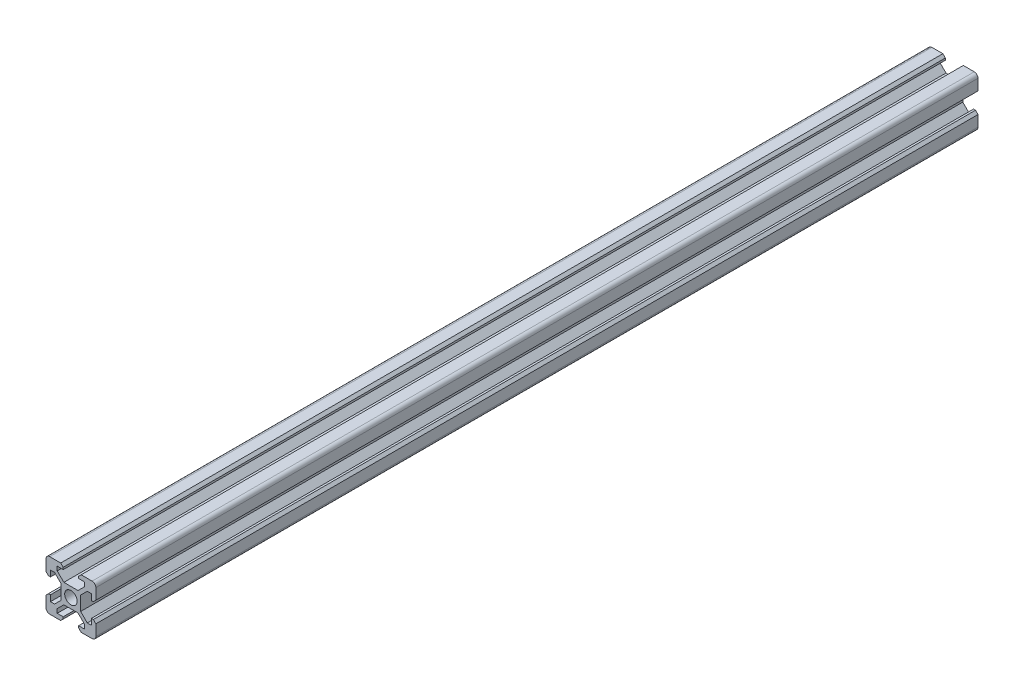
SolidWorks part; units mm, degrees
ref_plane "Front Plane" through (0, 0, 0) normal (0, 0, 1) x (1, 0, 0)
ref_plane "Top Plane" through (0, 0, 0) normal (0, 1, 0) x (1, 0, 0)
ref_plane "Right Plane" through (0, 0, 0) normal (1, 0, 0) x (0, 0, -1)
sketch "Sketch1" plane through (0, 0, 0) normal (0, 0, 1) x (1, 0, 0)
  line L0 (0, 16.1631) -> (0, -12.0251) construction
  line L1 (-21.8377, 0) -> (16.3885, 0) construction
  line L2 (2.8393, 3.9) -> (-2.8393, 3.9)
  line L3 (-2.8393, 3.9) -> (-5.5, 6.5607)
  line L4 (-5.5, 6.5607) -> (-5.5, 8.2)
  line L5 (-5.5, 8.2) -> (-3.1, 8.2)
  line L6 (-3.1, 8.2) -> (-3.1, 9)
  line L7 (-4.1, 10) -> (-8.5, 10)
  line L8 (-10, 8.5) -> (-10, 4.1)
  line L9 (-9, 3.1) -> (-8.2, 3.1)
  line L10 (-8.2, 3.1) -> (-8.2, 5.5)
  line L11 (-8.2, 5.5) -> (-6.5607, 5.5)
  line L12 (-6.5607, 5.5) -> (-3.9, 2.8393)
  line L13 (-3.9, 2.8393) -> (-3.9, -2.8393)
  line L14 (11.4015, -11.4015) -> (-14.8602, 14.8602) construction
  line L15 (-3.1, 9) -> (-4.1, 10)
  line L16 (-10, 4.1) -> (-9, 3.1)
  line L17 (-10, -4.1) -> (-9, -3.1)
  line L18 (-3.1, -9) -> (-4.1, -10)
  line L19 (-6.5607, -5.5) -> (-3.9, -2.8393)
  line L20 (-8.2, -5.5) -> (-6.5607, -5.5)
  line L21 (-8.2, -3.1) -> (-8.2, -5.5)
  line L22 (-9, -3.1) -> (-8.2, -3.1)
  line L23 (-10, -8.5) -> (-10, -4.1)
  line L24 (-4.1, -10) -> (-8.5, -10)
  line L25 (-3.1, -8.2) -> (-3.1, -9)
  line L26 (-5.5, -8.2) -> (-3.1, -8.2)
  line L27 (-5.5, -6.5607) -> (-5.5, -8.2)
  line L28 (-2.8393, -3.9) -> (-5.5, -6.5607)
  line L29 (2.8393, -3.9) -> (-2.8393, -3.9)
  line L30 (2.8393, -3.9) -> (5.5, -6.5607)
  line L31 (5.5, -6.5607) -> (5.5, -8.2)
  line L32 (5.5, -8.2) -> (3.1, -8.2)
  line L33 (3.1, -8.2) -> (3.1, -9)
  line L34 (4.1, -10) -> (8.5, -10)
  line L35 (10, -8.5) -> (10, -4.1)
  line L36 (9, -3.1) -> (8.2, -3.1)
  line L37 (8.2, -3.1) -> (8.2, -5.5)
  line L38 (8.2, -5.5) -> (6.5607, -5.5)
  line L39 (6.5607, -5.5) -> (3.9, -2.8393)
  line L40 (3.1, -9) -> (4.1, -10)
  line L41 (10, -4.1) -> (9, -3.1)
  line L42 (10, 4.1) -> (9, 3.1)
  line L43 (3.1, 9) -> (4.1, 10)
  line L44 (3.9, 2.8393) -> (3.9, -2.8393)
  line L45 (6.5607, 5.5) -> (3.9, 2.8393)
  line L46 (8.2, 5.5) -> (6.5607, 5.5)
  line L47 (8.2, 3.1) -> (8.2, 5.5)
  line L48 (9, 3.1) -> (8.2, 3.1)
  line L49 (10, 8.5) -> (10, 4.1)
  line L50 (4.1, 10) -> (8.5, 10)
  line L51 (3.1, 8.2) -> (3.1, 9)
  line L52 (5.5, 8.2) -> (3.1, 8.2)
  line L53 (5.5, 6.5607) -> (5.5, 8.2)
  line L54 (2.8393, 3.9) -> (5.5, 6.5607)
  circle A0 centre (0, 0) radius 2.5
  arc A1 (-10, 8.5) -> (-8.5, 10) centre (-8.5, 8.5) cw
  arc A2 (-10, -8.5) -> (-8.5, -10) centre (-8.5, -8.5) ccw
  arc A3 (10, -8.5) -> (8.5, -10) centre (8.5, -8.5) cw
  arc A4 (10, 8.5) -> (8.5, 10) centre (8.5, 8.5) ccw
  point P7 (3.1, -10)
  point P13 (-3.1, 10)
  point P15 (-10, 3.1)
  point P36 (-3.9, 0)
  point P44 (-10, -3.1)
  point P45 (-3.1, -10)
  point P53 (0, -3.9)
  point P76 (0, 3.9)
  point P77 (10, -3.1)
  point P78 (3.9, 0)
  point P79 (10, 3.1)
  point P80 (3.1, 10)
  dimension "D1" = 5
  dimension "D11" = 1.5
  dimension "D2" = 45
  dimension "D3" = 3.9
  dimension "D4" = 3.9
  dimension "D5" = 1.5
  dimension "D6" = 10
  dimension "D7" = 10
  dimension "D8" = 3.1
  dimension "D9" = 4.3
  dimension "D10" = 5.5
extrude "Boss-Extrude1" add sketch "Sketch1" along normal blind 354
